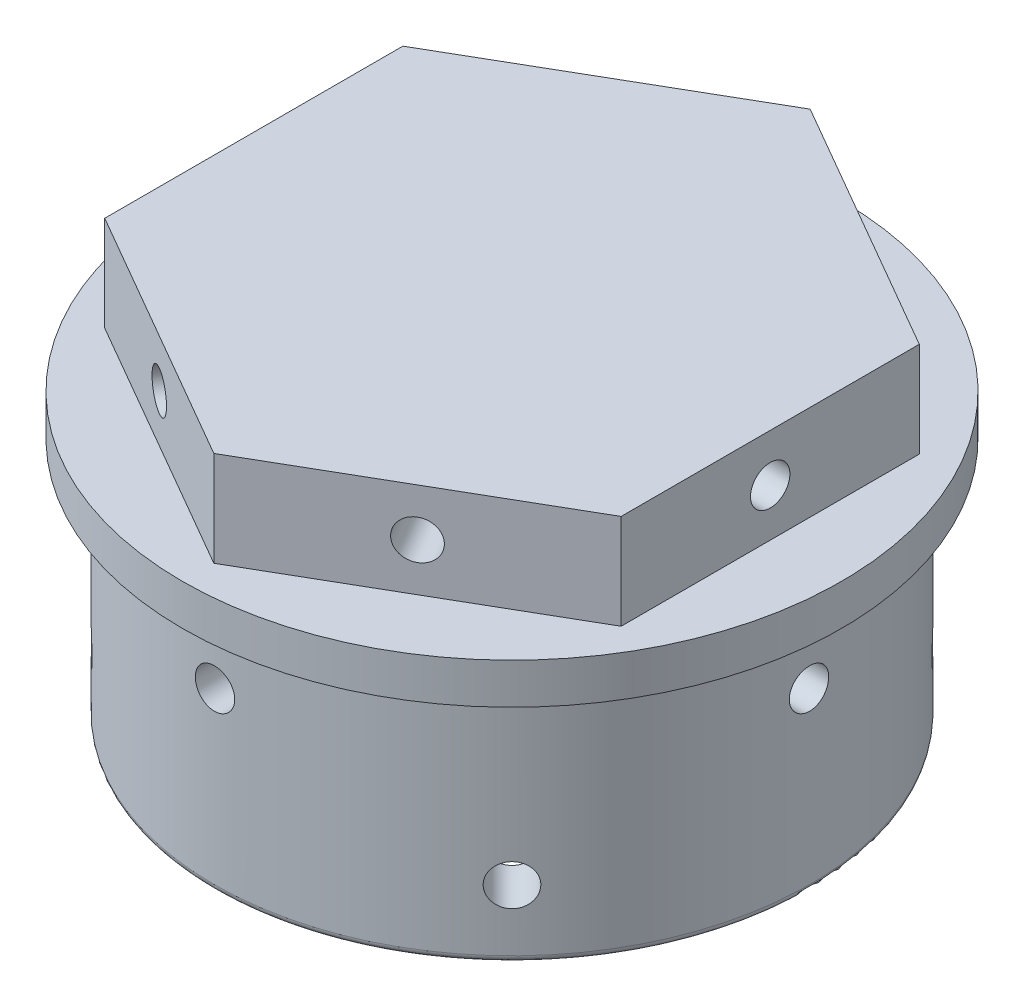
SolidWorks part; units mm, degrees
material "6061 合金"
ref_plane "前视基准面" through (0, 0, 0) normal (0, 0, 1) x (1, 0, 0)
ref_plane "上视基准面" through (0, 0, 0) normal (0, 1, 0) x (1, 0, 0)
ref_plane "右视基准面" through (0, 0, 0) normal (1, 0, 0) x (0, 0, -1)
sketch "草图1" plane through (0, 0, 0) normal (0, 1, 0) x (1, 0, 0)
  line L0 (0, 0) -> (0, 33.3478) construction
  line L1 (0, 0) -> (11.2563, 0) construction
  line L2 (-11.6913, -6.75) -> (0, 0) construction
  line L3 (0, 0) -> (11.6913, -6.75) construction
  line L4 (0, 0) -> (-10.5222, 6.075) construction
  line L5 (10.5222, 6.075) -> (0, 0) construction
  circle A0 centre (0, 0) radius 19
  circle A1 centre (0, 13.5) radius 1.45
  circle A2 centre (0, 0) radius 13.5 construction
  circle A3 centre (-11.6913, -6.75) radius 1.45
  circle A4 centre (11.6913, -6.75) radius 1.45
  circle A5 centre (0, 0) radius 12.15 construction
  circle A6 centre (-10.5222, 6.075) radius 2
  circle A7 centre (0, -12.15) radius 2
  circle A8 centre (10.5222, 6.075) radius 2
  dimension "D1" = 38
  dimension "D2" = 27
  dimension "D3" = 2.9
  dimension "D6" = 24.3
  dimension "D8" = 4
  dimension "D4" = 120
  dimension "D5" = 120
  dimension "D7" = 60
  dimension "D9" = 60
extrude "凸台-拉伸1" add sketch "草图1" along normal blind 12
sketch "草图2" plane through (0, 12, 0) normal (0, 1, 0) x (1, 0, 0)
  line L0 (0, 21.9393) -> (0, 0) construction
  line L1 (0, 21.9393) -> (-19, 10.9697)
  line L2 (-19, 10.9697) -> (-19, -10.9697)
  line L3 (-19, -10.9697) -> (0, -21.9393)
  line L4 (0, -21.9393) -> (19, -10.9697)
  line L5 (19, -10.9697) -> (19, 10.9697)
  line L6 (19, 10.9697) -> (0, 21.9393)
  circle A0 centre (0, 0) radius 19 construction
  circle A1 centre (0, 13.5) radius 1.45
  circle A2 centre (0, 13.5) radius 1.45 construction
  circle A3 centre (-10.5222, 6.075) radius 2
  circle A4 centre (-10.5222, 6.075) radius 2 construction
  circle A5 centre (10.5222, 6.075) radius 2
  circle A6 centre (10.5222, 6.075) radius 2 construction
  circle A7 centre (-11.6913, -6.75) radius 1.45
  circle A8 centre (-11.6913, -6.75) radius 1.45 construction
  circle A9 centre (0, -12.15) radius 2
  circle A10 centre (0, -12.15) radius 2 construction
  circle A11 centre (11.6913, -6.75) radius 1.45
  circle A12 centre (11.6913, -6.75) radius 1.45 construction
  dimension "D1" = 38
extrude "凸台-拉伸2" add sketch "草图2" against normal blind 7
sketch "草图3" plane through (9.5, 0, 16.4545) normal (0.5, 0, 0.866) x (0.866, 0, -0.5)
  line L1 (0, 12) -> (0, 5) construction
  line L2 (-10.9697, 12) -> (10.9697, 12) construction
  circle A1 centre (0, 8.5) radius 1.45
  dimension "D1" = 2.9
extrude "切除-拉伸1" cut sketch "草图3" against normal through all
sketch "草图4" plane through (-9.5, 0, 16.4545) normal (-0.5, 0, 0.866) x (0.866, 0, 0.5)
  line L0 (0, 5) -> (0, 12) construction
  line L1 (-10.9697, 12) -> (10.9697, 12) construction
  circle A0 centre (0, 8.5) radius 1.45
  dimension "D1" = 2.9
extrude "切除-拉伸2" cut sketch "草图4" against normal through all
sketch "草图5" plane through (-19, 0, 0) normal (-1, 0, 0) x (0, 0, 1)
  line L0 (0, 5) -> (0, 12) construction
  line L1 (-10.9697, 12) -> (10.9697, 12) construction
  circle A0 centre (0, 8.5) radius 1.45
  dimension "D1" = 2.9
extrude "切除-拉伸3" cut sketch "草图5" against normal through all
sketch "草图8" plane through (0, 0, 0) normal (0, -1, 0) x (1, 0, 0)
  circle A0 centre (0, 0) radius 24
  dimension "D1" = 48
extrude "切除-拉伸6" cut sketch "草图8" against normal up to surface (5 mm away) up to face at (16.5682, 5, 9.5656)
sketch "草图10" plane through (0, 5, 0) normal (0, -1, 0) x (1, 0, 0)
  circle A0 centre (0, 0) radius 24.25
  dimension "D1" = 48.5
extrude "凸台-拉伸3" add sketch "草图10" along normal blind 3
sketch "草图11" plane through (0, 2, 0) normal (0, -1, 0) x (1, 0, 0)
  circle A0 centre (0, 0) radius 21.9
  dimension "D1" = 43.8
extrude "凸台-拉伸4" add sketch "草图11" along normal blind 18
sketch "草图12" plane through (0, -16, 0) normal (0, -1, 0) x (1, 0, 0)
  line L8 (-15.6569, -9.799) -> (-9.799, -15.6569)
  line L9 (-4.1421, -18) -> (4.1421, -18)
  line L10 (9.799, -15.6569) -> (15.6569, -9.799)
  line L11 (18, -4.1421) -> (18, 4.1421)
  line L12 (15.6569, 9.799) -> (9.799, 15.6569)
  line L13 (4.1421, 18) -> (-4.1421, 18)
  line L14 (-9.799, 15.6569) -> (-15.6569, 9.799)
  line L15 (-18, 4.1421) -> (-18, -4.1421)
  circle A0 centre (0, 0) radius 18 construction
  arc A1 (-4.1421, 18) -> (-9.799, 15.6569) centre (-4.1421, 10) ccw
  arc A2 (9.799, 15.6569) -> (4.1421, 18) centre (4.1421, 10) ccw
  arc A3 (18, 4.1421) -> (15.6569, 9.799) centre (10, 4.1421) ccw
  arc A4 (15.6569, -9.799) -> (18, -4.1421) centre (10, -4.1421) ccw
  arc A5 (4.1421, -18) -> (9.799, -15.6569) centre (4.1421, -10) ccw
  arc A6 (-9.799, -15.6569) -> (-4.1421, -18) centre (-4.1421, -10) ccw
  arc A7 (-15.6569, -9.799) -> (-18, -4.1421) centre (-10, -4.1421) cw
  arc A8 (-15.6569, 9.799) -> (-18, 4.1421) centre (-10, 4.1421) ccw
  dimension "D1" = 36
  dimension "D2" = 8
extrude "切除-拉伸7" cut sketch "草图12" against normal blind 18
sketch "草图13" plane through (18, 0, 0) normal (-1, 0, 0) x (0, 0, 1)
  line L0 (-21.9, 2) -> (21.9, 2) construction
  circle A0 centre (0, -3) radius 1.45
  dimension "D2" = 2.9
  dimension "D1" = 5
sketch "草图14" plane through (12.7279, 0, -12.7279) normal (-0.7071, 0, 0.7071) x (0.7071, 0, 0.7071)
  line L0 (-21.9, -16) -> (21.9, -16) construction
  circle A0 centre (0, -11) radius 1.45
  dimension "D2" = 2.9
  dimension "D1" = 5
sketch "草图15" plane through (0, 0, -18) normal (0, 0, 1) x (1, 0, 0)
  line L0 (-21.9, 2) -> (21.9, 2) construction
  circle A0 centre (0, -3) radius 1.45
  dimension "D2" = 2.9
  dimension "D1" = 5
sketch "草图16" plane through (-12.7279, 0, -12.7279) normal (0.7071, 0, 0.7071) x (0.7071, 0, -0.7071)
  line L0 (-21.9, -16) -> (21.9, -16) construction
  circle A0 centre (0, -11) radius 1.5
  dimension "D1" = 3
  dimension "D2" = 5
extrude "切除-拉伸8" cut sketch "草图13" along normal through all and the other way through all
extrude "切除-拉伸9" cut sketch "草图14" against normal through all and the other way through all contours A0
extrude "切除-拉伸10" cut sketch "草图15" against normal through all and the other way through all contours A0
extrude "切除-拉伸11" cut sketch "草图16" against normal through all and the other way through all contours A0
fillet "圆角1" radius 0.5 17 edges at (0, -16, -21.9) (-12.7279, -16, 12.7279) (-17.391, -16, 7.2036) (-18, -16, 0) (-17.391, -16, -7.2036) (-12.7279, -16, -12.7279) (-7.2036, -16, -17.391) (0, -16, -18) (7.2036, -16, -17.391) (12.7279, -16, -12.7279) (17.391, -16, -7.2036) (18, -16, 0) (17.391, -16, 7.2036) (12.7279, -16, 12.7279) (7.2036, -16, 17.391) (0, -16, 18) (-7.2036, -16, 17.391)
fillet "圆角2" radius 2 16 edges at (0, 2, 18) (7.2036, 2, 17.391) (12.7279, 2, 12.7279) (17.391, 2, 7.2036) (18, 2, 0) (17.391, 2, -7.2036) (12.7279, 2, -12.7279) (7.2036, 2, -17.391) (0, 2, -18) (-7.2036, 2, -17.391) (-12.7279, 2, -12.7279) (-17.391, 2, -7.2036) (-18, 2, 0) (-17.391, 2, 7.2036) (-12.7279, 2, 12.7279) (-7.2036, 2, 17.391)
sketch "草图17" plane through (0, 12, 0) normal (0, 1, 0) x (1, 0, 0)
  circle A1 centre (0, 13.5) radius 1.45
  circle A2 centre (10.5222, 6.075) radius 2
  circle A3 centre (11.6913, -6.75) radius 1.45
  circle A4 centre (0, -12.15) radius 2
  circle A5 centre (-11.6913, -6.75) radius 1.45
  circle A6 centre (-10.5222, 6.075) radius 2.2726
extrude "凸台-拉伸5" add sketch "草图17" against normal blind 9
